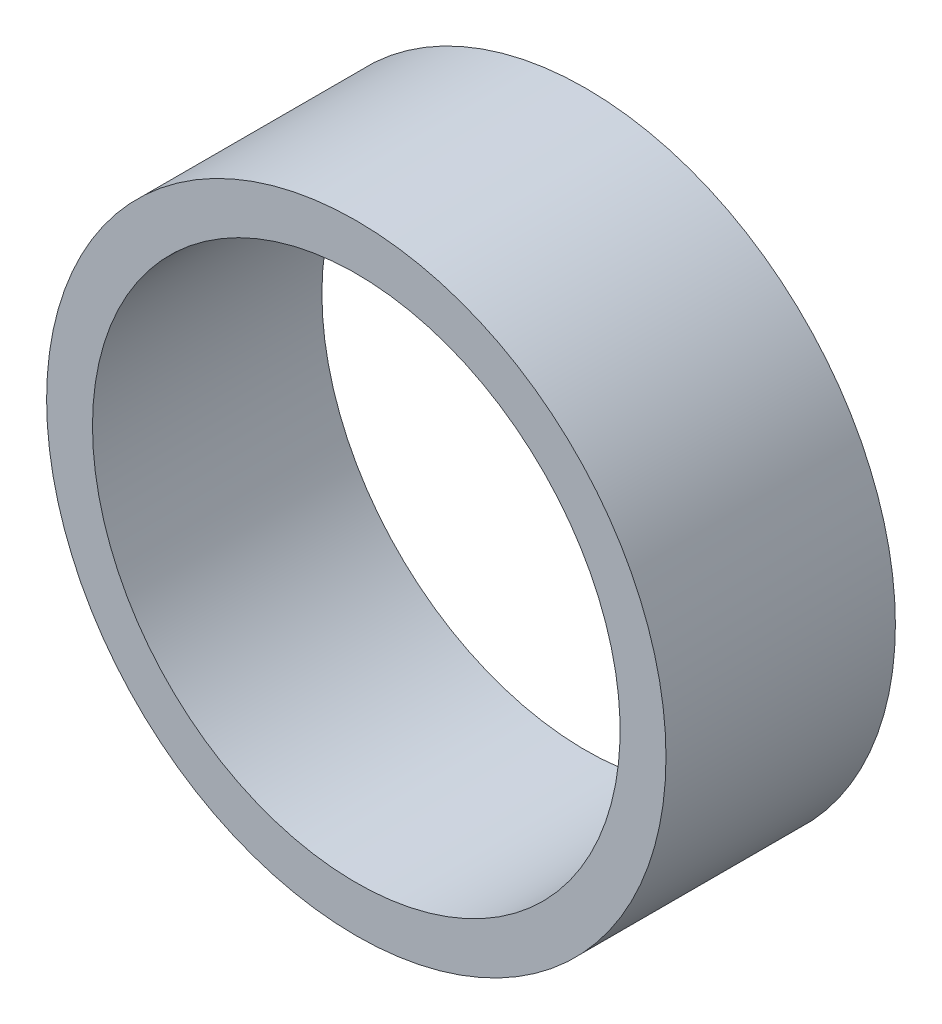
SolidWorks part; units mm, degrees
ref_plane "Front Plane" through (0, 0, 0) normal (0, 0, 1) x (1, 0, 0)
ref_plane "Top Plane" through (0, 0, 0) normal (0, 1, 0) x (1, 0, 0)
ref_plane "Right Plane" through (0, 0, 0) normal (1, 0, 0) x (0, 0, -1)
sketch "Sketch1" plane through (0, 0, 0) normal (0, 0, 1) x (1, 0, 0)
  circle A0 centre (0, 0) radius 1.35
  dimension "D1" = 2.7
extrude "Boss-Extrude1" add sketch "Sketch1" against normal blind 1
sketch "Sketch2" plane through (0, 0, -1) normal (0, 0, -1) x (-1, 0, 0)
  circle A0 centre (0, 0) radius 1.15
  dimension "D1" = 2.3
extrude "Cut-Extrude1" cut sketch "Sketch2" against normal through all
